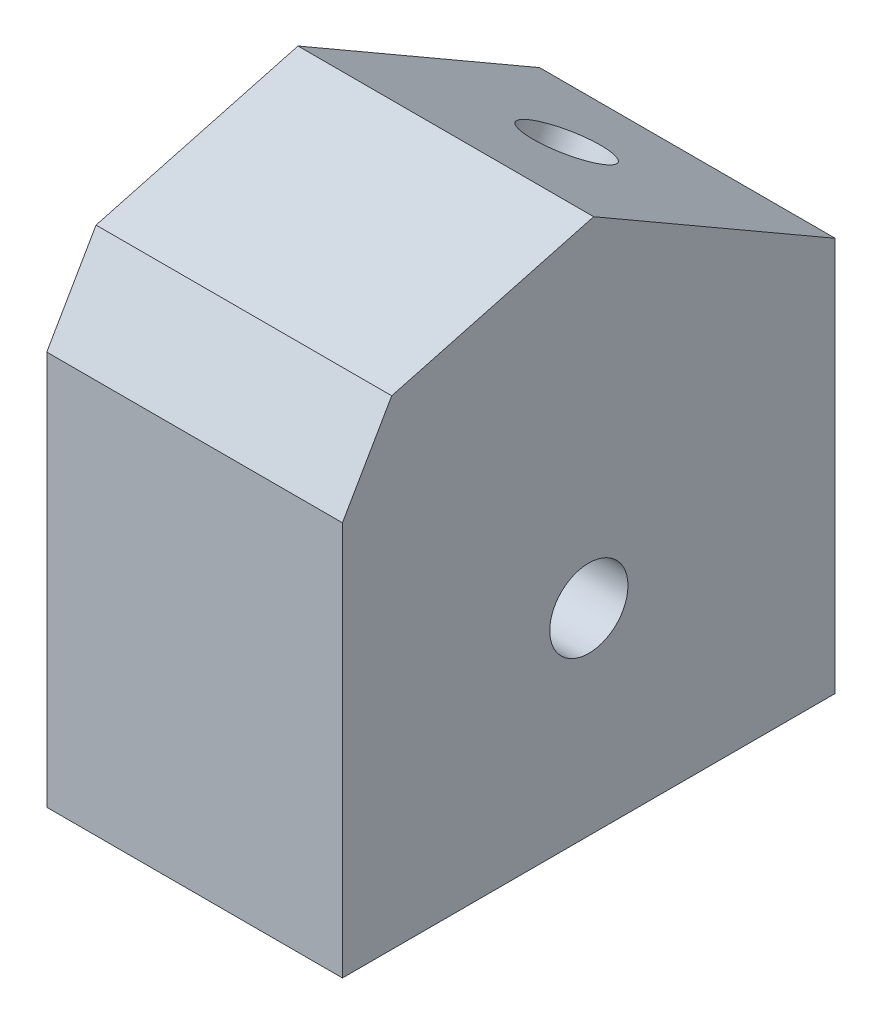
SolidWorks part; units mm, degrees
material "ABS"
ref_plane "Plano frontal" through (0, 0, 0) normal (0, 0, 1) x (1, 0, 0)
ref_plane "Plano superior" through (0, 0, 0) normal (0, 1, 0) x (1, 0, 0)
ref_plane "Plano direito" through (0, 0, 0) normal (1, 0, 0) x (0, 0, -1)
sketch "Esboço1" plane through (0, 0, 0) normal (1, 0, 0) x (0, 0, -1)
  line L0 (0, 0) -> (25, 0) construction
  line L1 (25, -20) -> (-25, -20)
  line L2 (25, -20) -> (25, 20)
  line L4 (-25, -20) -> (-25, 20)
  line L5 (25, -20) -> (-25, 20) construction
  line L6 (25, 20) -> (-25, -20) construction
  line L8 (-12.5, 41.6506) -> (25, 20)
  line L9 (25, 20) -> (-25, 20) construction
  line L11 (-25, 20) -> (-12.5, 41.6506)
  circle A0 centre (0, 0) radius 3.97
  point P1 (0, 0)
  dimension "D3" = 7.94
  dimension "D1" = 40
  dimension "D2" = 50
  dimension "D4" = 30
  dimension "D5" = 90
extrude "Ressalto-extrusão1" add sketch "Esboço1" along normal mid plane 30
sketch "Esboço2" plane through (0, 25.8253, -14.9103) normal (0, 0.866, -0.5) x (-1, 0, 0)
  line L0 (0, -11.6506) -> (0, 31.6506) construction
  line L1 (-15, -11.6506) -> (15, -11.6506) construction
  line L2 (-15, 31.6506) -> (15, 31.6506) construction
  line L3 (15, 10) -> (-15, 10) construction
  line L4 (15, -11.6506) -> (15, 31.6506) construction
  line L5 (-15, -11.6506) -> (-15, 31.6506) construction
sketch "Esboço3" plane through (0, 0, -25) normal (0, 0, -1) x (-1, 0, 0)
  circle A0 centre (0, 0) radius 3.97
  dimension "D1" = 7.94
extrude "Corte-extrusão2" cut sketch "Esboço3" against normal blind 25
chamfer "Chanfro1" distance 15 angle 45 1 edges at (0, 41.6506, 12.5)
sketch "Esboço4" plane through (0, 25.8253, -14.9103) normal (0, 0.866, -0.5) x (1, 0, 0)
  line L0 (0, 11.6506) -> (0, -16.6506) construction
  line L1 (-15, -16.6506) -> (15, -16.6506) construction
  line L2 (15, -2.5) -> (-15, -2.5) construction
  line L3 (15, 11.6506) -> (15, -16.6506) construction
  line L4 (-15, 11.6506) -> (-15, -16.6506) construction
  circle A0 centre (0, -2.5) radius 3.97
  dimension "D1" = 7.94
extrude "Corte-extrusão3" cut sketch "Esboço4" against normal blind 15
